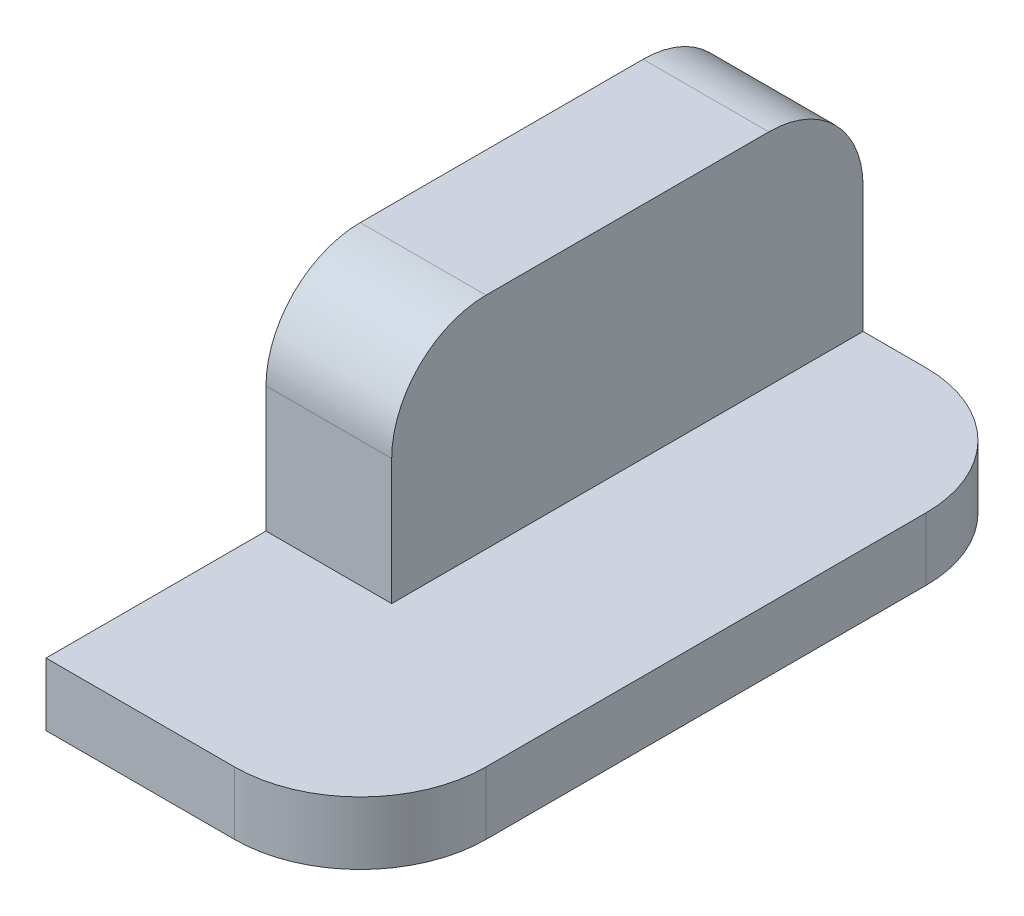
SolidWorks part; units mm, degrees
ref_plane "정면" through (0, 0, 0) normal (0, 0, 1) x (1, 0, 0)
ref_plane "윗면" through (0, 0, 0) normal (0, 1, 0) x (1, 0, 0)
ref_plane "우측면" through (0, 0, 0) normal (1, 0, 0) x (0, 0, -1)
sketch "스케치1" plane through (0, 0, 0) normal (1, 0, 0) x (0, 0, -1)
  line L0 (0, 0) -> (35, 0)
  line L1 (0, 0) -> (0, -10)
  line L2 (0, -10) -> (110, -10)
  line L3 (110, -10) -> (110, 35)
  line L4 (110, 35) -> (35, 35)
  line L5 (35, 35) -> (35, 0)
  dimension "D1" = 110
  dimension "D2" = 10
  dimension "D3" = 45
  dimension "D4" = 75
extrude "보스-돌출1" add sketch "스케치1" along normal blind 50
sketch "스케치2" plane through (0, 0, -35) normal (0, 0, 1) x (1, 0, 0)
  line L0 (50, 35) -> (0, 35) construction
  line L1 (50, 0) -> (20, 0)
  line L2 (50, 0) -> (50, 35)
  line L3 (50, 35) -> (20, 35)
  line L4 (20, 0) -> (20, 35)
  dimension "D1" = 30
extrude "컷-돌출1" cut sketch "스케치2" against normal blind 116
fillet "필렛1" radius 15 2 edges at (10, 35, -110) (10, 35, -35)
fillet "필렛2" radius 20 2 edges at (50, -5, -110) (50, -5, 0)
